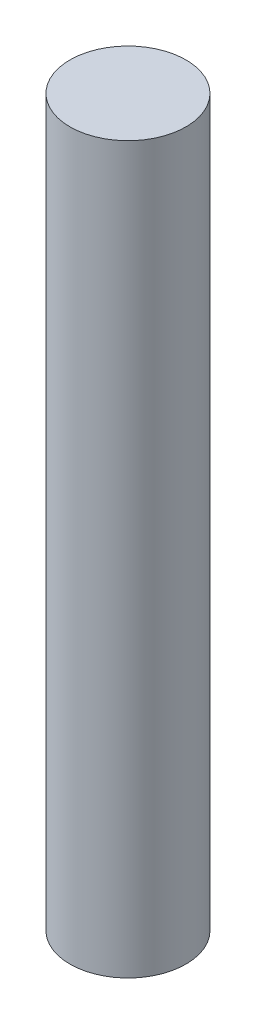
SolidWorks part; units mm, degrees
ref_plane "Front Plane" through (0, 0, 0) normal (0, 0, 1) x (1, 0, 0)
ref_plane "Top Plane" through (0, 0, 0) normal (0, 1, 0) x (1, 0, 0)
ref_plane "Right Plane" through (0, 0, 0) normal (1, 0, 0) x (0, 0, -1)
sketch "Sketch1" plane through (0, 0, 0) normal (0, 1, 0) x (1, 0, 0)
  circle A0 centre (0, 0) radius 10
  dimension "D1" = 20
extrude "Boss-Extrude1" add sketch "Sketch1" along normal blind 125
